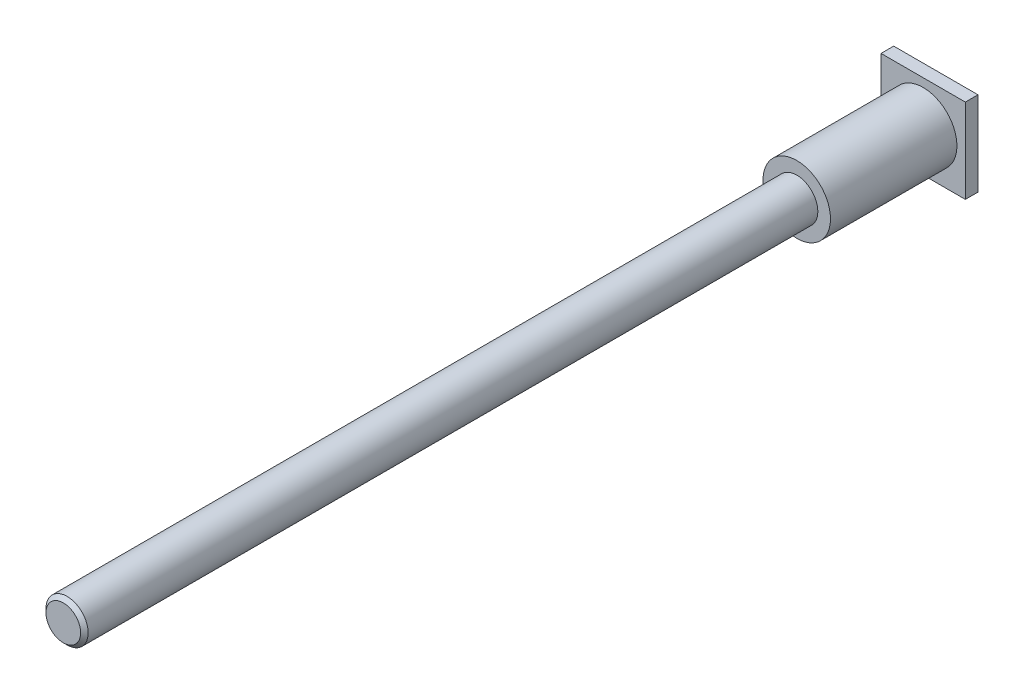
SolidWorks part; units mm, degrees
material "Сталь"
ref_plane "Спереди" through (0, 0, 0) normal (0, 0, 1) x (1, 0, 0)
ref_plane "Сверху" through (0, 0, 0) normal (0, 1, 0) x (1, 0, 0)
ref_plane "Справа" through (0, 0, 0) normal (1, 0, 0) x (0, 0, -1)
sketch "Эскиз1" plane through (0, 0, 0) normal (0, 0, 1) x (1, 0, 0)
  circle A0 centre (0, 0) radius 4
  dimension "D1" = 8
extrude "Бобышка-Вытянуть1" add sketch "Эскиз1" along normal blind 102
sketch "Эскиз2" plane through (0, 0, 0) normal (0, 0, -1) x (-1, 0, 0)
  line L1 (5, -5) -> (-5, -5)
  line L2 (5, -5) -> (5, 5)
  line L3 (5, 5) -> (-5, 5)
  line L4 (-5, -5) -> (-5, 5)
  line L5 (5, -5) -> (-5, 5) construction
  line L6 (5, 5) -> (-5, -5) construction
  point P0 (0, 0)
  dimension "D1" = 10
extrude "Бобышка-Вытянуть2" add sketch "Эскиз2" along normal blind 1.5
sketch "Эскиз6" plane through (0, 0, -1.5) normal (0, 0, -1) x (-1, 0, 0)
  circle A0 centre (0, 0) radius 2.055
  dimension "D1" = 4.11
extrude "Вырез-Вытянуть1" cut sketch "Эскиз6" against normal blind 15
cosmetic thread "Условное изображение резьбы1" parameters "D1"=13, "D2"=5
sketch "Эскиз7" plane through (0, 0, 13.5) normal (0, 0, -1) x (-1, 0, 0)
  circle A1 centre (0, 0) radius 2.055
  circle A2 centre (0, 0) radius 2.055
  dimension "D1" = 0
extrude "Вырез-Вытянуть2" cut sketch "Эскиз7" against normal blind 1.2 draft 60
chamfer "Фаска1" distance 0.445 angle 45 1 edges at (-2.055, 0, -1.5)
sketch "Эскиз9" plane through (0, 0, 0) normal (0, 0, 1) x (1, 0, 0)
  circle A0 centre (0, 0) radius 2.5
  circle A1 centre (0, 0) radius 10
  dimension "D1" = 5
  dimension "D2" = 20
extrude "Вырез-Вытянуть3" cut sketch "Эскиз9" along normal through all from offset 15
cosmetic thread "Cosmetic Thread1" parameters "D1"=20, "D2"=4.11
chamfer "Chamfer1" distance 0.445 angle 45 1 edges at (2.5, 0, 102)
